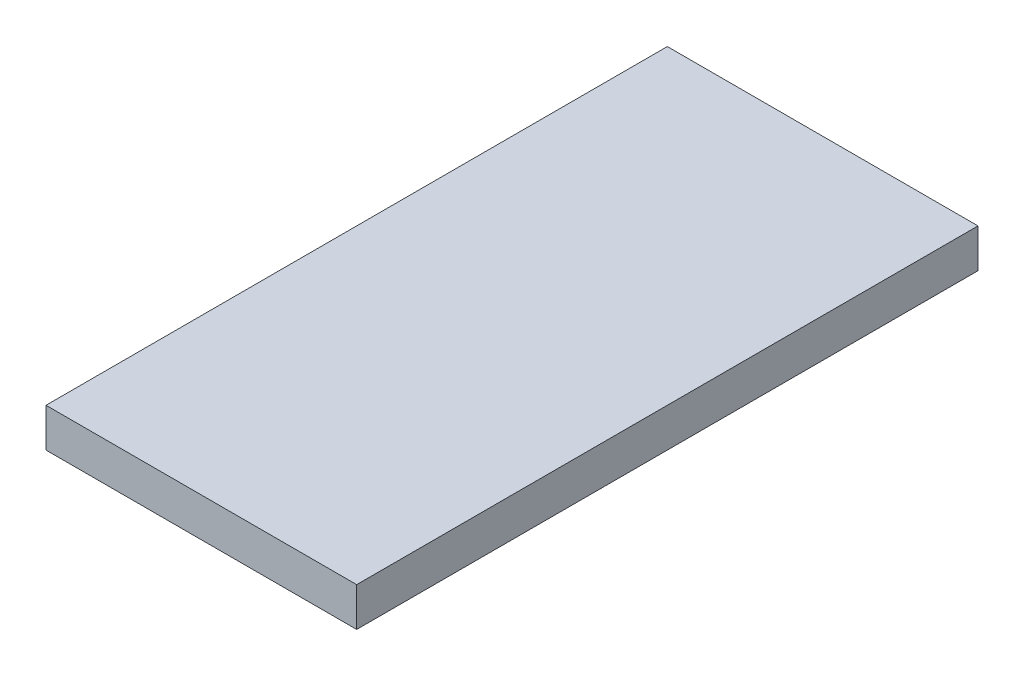
SolidWorks part; units mm, degrees
ref_plane "Front Plane" through (0, 0, 0) normal (0, 0, 1) x (1, 0, 0)
ref_plane "Top Plane" through (0, 0, 0) normal (0, 1, 0) x (1, 0, 0)
ref_plane "Right Plane" through (0, 0, 0) normal (1, 0, 0) x (0, 0, -1)
sketch "Sketch1" plane through (0, 0, 0) normal (0, 1, 0) x (1, 0, 0)
  line L1 (-304.8, -609.6) -> (304.8, -609.6)
  line L2 (-304.8, -609.6) -> (-304.8, 609.6)
  line L3 (-304.8, 609.6) -> (304.8, 609.6)
  line L4 (304.8, -609.6) -> (304.8, 609.6)
  line L5 (-304.8, -609.6) -> (304.8, 609.6) construction
  line L6 (-304.8, 609.6) -> (304.8, -609.6) construction
  point P0 (0, 0)
extrude "Boss-Extrude1" add sketch "Sketch1" along normal mid plane 76.2
